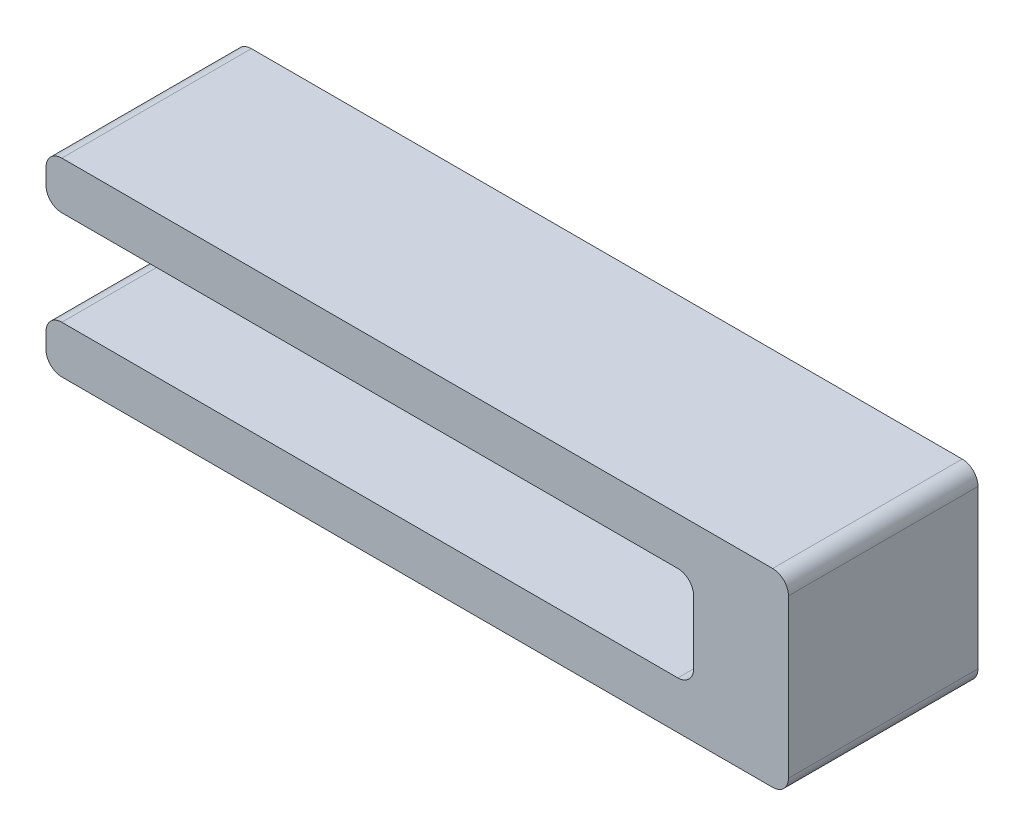
SolidWorks part; units mm, degrees
ref_plane "Front Plane" through (0, 0, 0) normal (0, 0, 1) x (1, 0, 0)
ref_plane "Top Plane" through (0, 0, 0) normal (0, 1, 0) x (1, 0, 0)
ref_plane "Right Plane" through (0, 0, 0) normal (1, 0, 0) x (0, 0, -1)
sketch "Sketch2" plane through (0, 0, 0) normal (0, 0, 1) x (1, 0, 0)
  line L1 (0, 0) -> (23.5, 0)
  line L2 (0, 0) -> (0, 6)
  line L3 (0, 6) -> (23.5, 6)
  line L4 (23.5, 0) -> (23.5, 6)
  line L5 (0, 4.5) -> (20.5, 4.5)
  line L6 (0, 4.5) -> (0, 1.5)
  line L7 (0, 1.5) -> (20.5, 1.5)
  line L8 (20.5, 4.5) -> (20.5, 1.5)
  dimension "D1" = 6
  dimension "D2" = 3
  dimension "D3" = 1.5
  dimension "D4" = 3
  dimension "D5" = 20.5
extrude "Boss-Extrude1" add sketch "Sketch2" along normal blind 6 contours L5 L8 L7 L2 L1 L4 L3
fillet "Fillet1" radius 0.5 8 edges at (20.5, 4.5, 3) (23.5, 6, 3) (20.5, 1.5, 3) (23.5, 0, 3) (0, 0, 3) (0, 1.5, 3) (0, 4.5, 3) (0, 6, 3)
